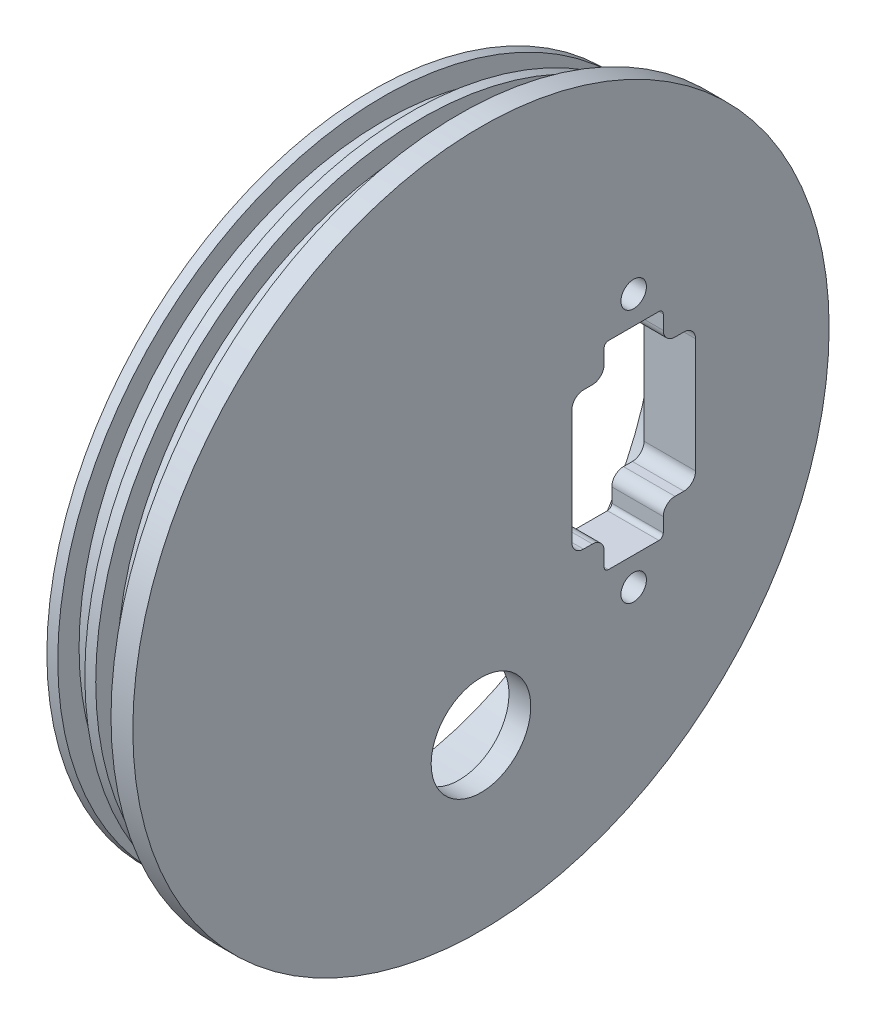
SolidWorks part; units mm, degrees
material "6061 Alloy"
ref_plane "Front" through (0, 0, 0) normal (0, 0, 1) x (1, 0, 0)
ref_plane "Top" through (0, 0, 0) normal (0, 1, 0) x (1, 0, 0)
ref_plane "Right" through (0, 0, 0) normal (1, 0, 0) x (0, 0, -1)
sketch "Sketch1" plane through (0, 0, 0) normal (0, 0, 1) x (1, 0, 0)
  line L0 (4.318, 50.673) -> (4.318, 47.371)
  line L1 (-8.3185, 47.371) -> (-6.731, 47.371)
  line L2 (-8.3185, 47.371) -> (-8.3185, 41.0972)
  line L3 (-8.3185, 41.0972) -> (0, 41.0972)
  line L4 (0, 41.0972) -> (0, 0)
  line L5 (0, 0) -> (7.493, 0)
  line L6 (7.493, 0) -> (7.493, 50.673)
  line L7 (7.493, 50.673) -> (4.318, 50.673)
  line L8 (-6.731, 47.371) -> (-6.731, 44.2722)
  line L9 (-6.731, 44.2722) -> (-2.794, 44.2722)
  line L10 (-2.794, 44.2722) -> (-2.794, 47.371)
  line L11 (-2.794, 47.371) -> (-1.2065, 47.371)
  line L12 (-1.2065, 47.371) -> (-1.2065, 44.2722)
  line L13 (-1.2065, 44.2722) -> (2.7305, 44.2722)
  line L14 (2.7305, 44.2722) -> (2.7305, 47.371)
  line L15 (2.7305, 47.371) -> (4.318, 47.371)
  dimension "D1" = 3.175
  dimension "D2" = 50.673
  dimension "D3" = 3.302
  dimension "D4" = 3.937
  dimension "D5" = 7.493
  dimension "D6" = 3.175
  dimension "D7" = 1.5875
  dimension "D8" = 3.0988
revolve "Revolve1" add sketch "Sketch1" angle 360 about L5
sketch "Sketch6" plane through (7.493, 0, 0) normal (1, 0, 0) x (0, 0, -1)
  line L0 (22.225, 14.4272) -> (22.225, -14.4272) construction
  line L1 (18.5547, 14.4272) -> (25.8953, 14.4272)
  line L2 (13.2207, 8.3312) -> (13.2207, -8.3312)
  line L3 (18.5547, -14.4272) -> (25.8953, -14.4272)
  line L4 (31.2293, 8.3312) -> (31.2293, -8.3312)
  line L5 (14.9225, 10.033) -> (16.2179, 10.033)
  line L6 (17.9197, 11.7348) -> (17.9197, 13.7922)
  line L7 (26.5303, 13.7922) -> (26.5303, 11.7348)
  line L8 (28.2321, 10.033) -> (29.5275, 10.033)
  line L9 (29.5275, -10.033) -> (28.2321, -10.033)
  line L10 (26.5303, -11.7348) -> (26.5303, -13.7922)
  line L11 (17.9197, -13.7922) -> (17.9197, -11.7348)
  line L12 (16.2179, -10.033) -> (14.9225, -10.033)
  line L13 (22.225, 14.4272) -> (22.225, 18.4785) construction
  line L14 (22.225, -14.4272) -> (22.225, -18.4785) construction
  arc A0 (17.9197, -11.7348) -> (16.2179, -10.033) centre (16.2179, -11.7348) ccw
  arc A1 (28.2321, -10.033) -> (26.5303, -11.7348) centre (28.2321, -11.7348) ccw
  arc A2 (26.5303, 11.7348) -> (28.2321, 10.033) centre (28.2321, 11.7348) ccw
  arc A3 (16.2179, 10.033) -> (17.9197, 11.7348) centre (16.2179, 11.7348) ccw
  arc A5 (13.2207, 8.3312) -> (14.9225, 10.033) centre (14.9225, 8.3312) cw
  arc A6 (14.9225, -10.033) -> (13.2207, -8.3312) centre (14.9225, -8.3312) cw
  arc A7 (29.5275, -10.033) -> (31.2293, -8.3312) centre (29.5275, -8.3312) ccw
  arc A8 (29.5275, 10.033) -> (31.2293, 8.3312) centre (29.5275, 8.3312) cw
  arc A9 (17.9197, -13.7922) -> (18.5547, -14.4272) centre (18.5547, -13.7922) ccw
  arc A10 (26.5303, -13.7922) -> (25.8953, -14.4272) centre (25.8953, -13.7922) cw
  arc A11 (26.5303, 13.7922) -> (25.8953, 14.4272) centre (25.8953, 13.7922) ccw
  arc A12 (18.5547, 14.4272) -> (17.9197, 13.7922) centre (18.5547, 13.7922) ccw
  circle A13 centre (22.225, 18.4785) radius 1.8542
  circle A14 centre (22.225, -18.4785) radius 1.8542
  point P4 (31.2293, 0)
  point P28 (13.2207, 10.033)
  point P31 (13.2207, -10.033)
  point P38 (17.9197, -14.4272)
  point P41 (26.5303, -14.4272)
  dimension "D8" = 1.7018
  dimension "D9" = 1.7018
  dimension "D10" = 0.635
  dimension "D11" = 3.7084
  dimension "D1" = 18.0086
  dimension "D2" = 28.8544
  dimension "D3" = 20.066
  dimension "D6" = 22.225
  dimension "D7" = 8.6106
  dimension "D12" = 36.957
extrude "Cut-Extrude1" cut sketch "Sketch6" against normal through all
hole_wizard "#6-32 Tapped Hole1" positions "Sketch8" profile "Sketch7" tap size "#6-32" standard "ANSI Inch"
sketch "Sketch8" plane through (0, 0, 0) normal (-1, 0, 0) x (0, 0, 1)
  line L0 (0, 0) -> (0, 14.4348) construction
  point P2 (0, 14.4348)
  point P8 (0, 0.5486)
  dimension "D1" = 14.4348
  dimension "D2" = 0.5486
sketch "Sketch7" plane through (0, 14.4348, 0) normal (0, 1, 0) x (0, 0, 1)
  line L0 (0, 0) -> (0, 5.1307)
  line L1 (0, 5.1307) -> (1.3525, 4.318)
  line L2 (1.3525, 4.318) -> (1.3525, 0)
  line L5 (1.3525, 0) -> (0, 0)
  line L10 (0, 5.1307) -> (-1.3526, 4.318) construction
  line L11 (0, -6.35) -> (0, 107.95) construction
  dimension "Tap Drill Dia." = 2.7051
  dimension "Tap Drill Depth" = 4.318
  dimension "Drill Angle" = 118
sketch "Sketch12" plane through (7.493, 0, 0) normal (1, 0, 0) x (0, 0, -1)
  circle A0 centre (0, -26.016) radius 15.0813
  circle A1 centre (0, 0) radius 41.0972 construction
  dimension "D1" = 30.1625
extrude "Cut-Extrude3" cut sketch "Sketch12" against normal through all from offset 3.175 contours A0 offset against normal yes
hole_wizard "M16x1.5 Tapped Hole1" positions "Sketch14" profile "Sketch15" tap size "M16x1.5" standard "ANSI Metric" end condition through all
sketch "Sketch14" plane through (4.318, 0, 0) normal (-1, 0, 0) x (0, 0, 1)
  point P5 (0, -26.016)
sketch "Sketch15" plane through (4.318, -26.016, 0) normal (0, 1, 0) x (0, 0, 1)
  line L0 (0, 0) -> (0, 3.175)
  line L1 (0, 3.175) -> (7.25, 3.175)
  line L2 (7.25, 3.175) -> (7.25, 0)
  line L5 (7.25, 0) -> (0, 0)
  line L11 (0, -6.35) -> (0, 107.95) construction
  dimension "Thread Major Dia." = 14.5
  dimension "Thru Tap Drill Depth" = 3.175
